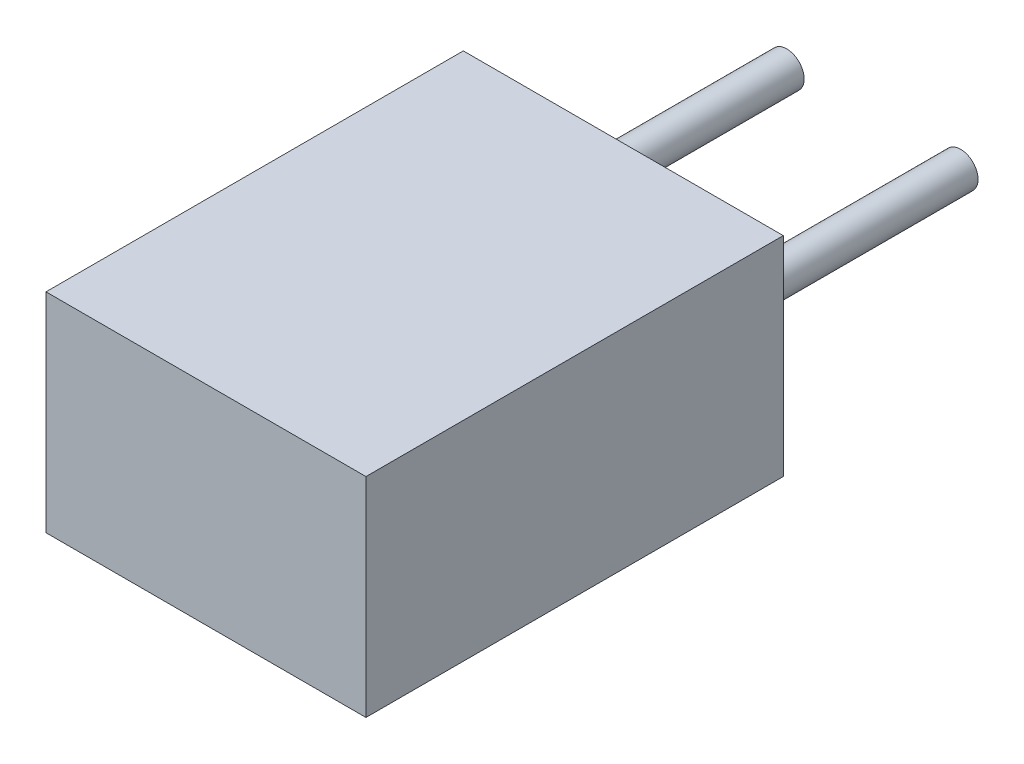
SolidWorks part; units mm, degrees
ref_plane "Plan de face" through (0, 0, 0) normal (0, 0, 1) x (1, 0, 0)
ref_plane "Plan de dessus" through (0, 0, 0) normal (0, 1, 0) x (1, 0, 0)
ref_plane "Plan de droite" through (0, 0, 0) normal (1, 0, 0) x (0, 0, -1)
sketch "Esquisse1" plane through (0, 0, 0) normal (0, 0, 1) x (1, 0, 0)
  line L1 (-2.3, -1.5) -> (2.3, -1.5)
  line L2 (-2.3, -1.5) -> (-2.3, 1.5)
  line L3 (-2.3, 1.5) -> (2.3, 1.5)
  line L4 (2.3, -1.5) -> (2.3, 1.5)
  line L5 (-2.3, -1.5) -> (2.3, 1.5) construction
  line L6 (-2.3, 1.5) -> (2.3, -1.5) construction
  point P0 (0, 0)
  dimension "D1" = 3
  dimension "D2" = 4.6
extrude "Boss.-Extru.1" add sketch "Esquisse1" along normal blind 6
sketch "Esquisse2" plane through (0, 0, 0) normal (0, 0, -1) x (-1, 0, 0)
  line L0 (-1.25, 0) -> (0, 0) construction
  line L1 (0, 0) -> (1.25, 0) construction
  circle A0 centre (-1.25, 0) radius 0.25
  circle A1 centre (1.25, 0) radius 0.25
  dimension "D1" = 0.5
  dimension "D2" = 2.5
extrude "Boss.-Extru.2" add sketch "Esquisse2" along normal blind 3.6
